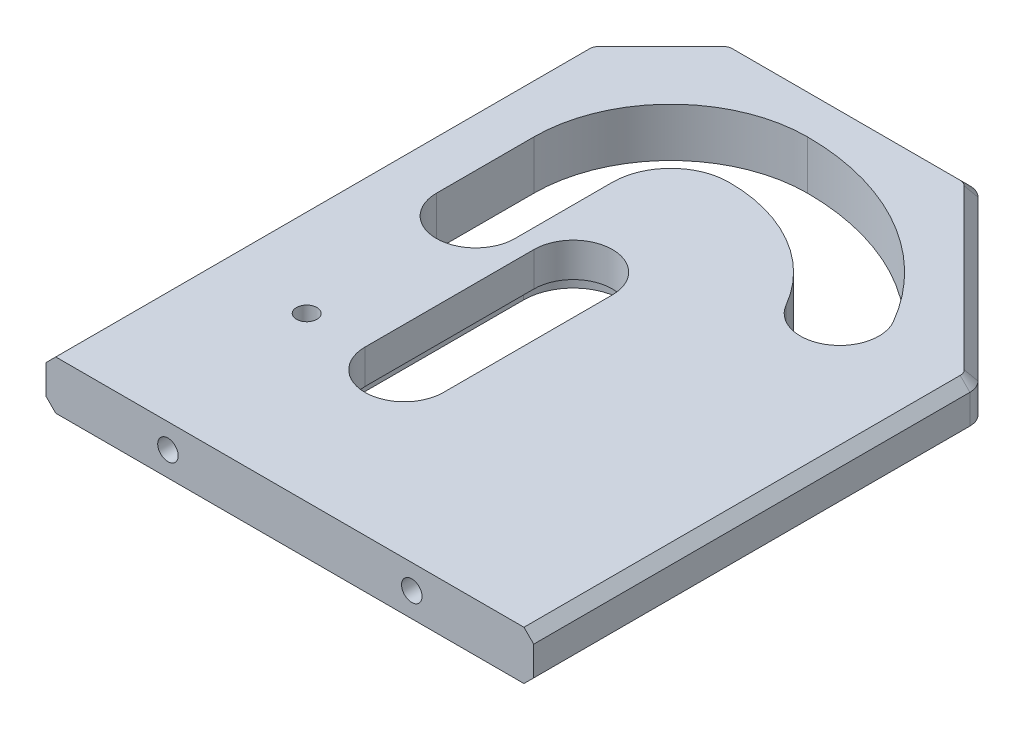
SolidWorks part; units mm, degrees
ref_plane "Front Plane" through (0, 0, 0) normal (0, 0, 1) x (1, 0, 0)
ref_plane "Top Plane" through (0, 0, 0) normal (0, 1, 0) x (1, 0, 0)
ref_plane "Right Plane" through (0, 0, 0) normal (1, 0, 0) x (0, 0, -1)
sketch "Sketch1" plane through (0, 0, 0) normal (0, 1, 0) x (1, 0, 0)
  line L1 (-40, -68.0944) -> (60, -68.0944)
  line L2 (-40, -68.0944) -> (-40, 58)
  line L3 (-40, 58) -> (60, 58)
  line L4 (60, -68.0944) -> (60, 58)
  dimension "D1" = 68.0944
  dimension "D2" = 40
  dimension "D3" = 58
  dimension "D4" = 60
extrude "Boss-Extrude1" add sketch "Sketch1" along normal mid plane 10
sketch "Slots Path" plane through (0, 0, 0) normal (0, 1, 0) x (1, 0, 0)
  line L2 (-20, 0) -> (-20, 20)
  line L3 (0, 0) -> (0, -34.641)
  line L4 (-5.5, 0) -> (5.5, 0) construction
  arc A1 (0, 40) -> (-20, 20) centre (0, 20) ccw
  arc A2 (0, 40) -> (34.641, 20) centre (0, 0) cw
  point P1 (-20, -34.641)
  dimension "D1" = 20
  dimension "D2" = 40
  dimension "D3" = 20
  dimension "D4" = 20
  dimension "D5" = 40
sketch "Sketch3" plane through (0, 5, 0) normal (0, 1, 0) x (1, 0, 0)
  line L9 (-8.05, 0) -> (-8.05, -34.641)
  line L10 (-11.95, 0) -> (-11.95, 20)
  line L11 (-28.05, 0) -> (-28.05, 20)
  line L12 (8.05, 0) -> (8.05, -34.641)
  arc A2 (-8.05, 0) -> (8.05, 0) centre (0, 0) cw
  arc A3 (-8.05, -34.641) -> (8.05, -34.641) centre (0, -34.641) ccw
  arc A18 (0, 31.95) -> (-11.95, 20) centre (0, 20) ccw
  arc A19 (27.6695, 15.975) -> (0, 31.95) centre (0, 0) ccw
  arc A20 (0, 48.05) -> (-28.05, 20) centre (0, 20) ccw
  arc A21 (41.6125, 24.025) -> (0, 48.05) centre (0, 0) ccw
  arc A22 (-11.95, 0) -> (-28.05, 0) centre (-20, 0) cw
  arc A23 (27.6695, 15.975) -> (41.6125, 24.025) centre (34.641, 20) ccw
extrude "Slots" cut sketch "Sketch3" against normal through all
sketch "Sketch12" plane through (0, -5, 0) normal (0, -1, 0) x (1, 0, 0)
  line L2 (10.15, 0) -> (10.15, 34.641)
  line L3 (-10.15, 0) -> (-10.15, 34.641)
  arc A0 (10.15, 0) -> (-10.15, 0) centre (0, 0) cw
  arc A1 (10.15, 34.641) -> (-10.15, 34.641) centre (0, 34.641) ccw
extrude "Cut-Extrude6" cut sketch "Sketch12" against normal blind 3
hole_wizard "M5x0.8 Tapped Hole2" positions "Sketch8" profile "Sketch9" tap size "M5x0.8" standard "ANSI Metric" end condition through all
sketch "Sketch8" plane through (0, 5, 0) normal (0, 1, 0) x (1, 0, 0)
  point P0 (-20, -34.641)
cosmetic thread "Hole Thread3" parameters "D2"=5
sketch "Sketch9" plane through (-20, 5, 34.641) normal (1, 0, 0) x (0, 0, 1)
  line L0 (0, 0) -> (0, 10)
  line L1 (0, 10) -> (2.1, 10)
  line L2 (2.1, 10) -> (2.1, 0)
  line L5 (2.1, 0) -> (0, 0)
  line L11 (0, -6.35) -> (0, 107.95) construction
  dimension "Thru Tap Drill Dia." = 4.2
  dimension "Thru Tap Drill Depth" = 10
sketch "Sketch13" plane through (0, -5, 0) normal (0, -1, 0) x (1, 0, 0)
  circle A0 centre (-20, 34.641) radius 4.15
  dimension "D1" = 8.3
extrude "Cut-Extrude7" cut sketch "Sketch13" against normal blind 5
hole_wizard "M5x0.8 Tapped Hole1" positions "Sketch6" profile "Sketch7" tap size "M5x0.8" standard "ANSI Metric"
sketch "Sketch6" plane through (0, 0, 68.0944) normal (0, 0, 1) x (1, 0, 0)
  line L0 (55, 0) -> (-55, 0) construction
  line L1 (-40, 5) -> (-40, -5) construction
  line L2 (60, 5) -> (60, -5) construction
  point P0 (-15, 0)
  point P2 (35, 0)
  point P11 (-40, 0)
  dimension "D1" = 25
  dimension "D2" = 25
sketch "Sketch7" plane through (-15, 0, 68.0944) normal (1, 0, 0) x (0, -1, 0)
  line L0 (0, 0) -> (0, 21.2618)
  line L1 (0, 21.2618) -> (2.1, 20)
  line L2 (2.1, 20) -> (2.1, 0)
  line L5 (2.1, 0) -> (0, 0)
  line L10 (0, 21.2618) -> (-2.1, 20) construction
  line L11 (0, -6.35) -> (0, 107.95) construction
  dimension "Tap Drill Dia." = 4.2
  dimension "Tap Drill Depth" = 20
  dimension "Drill Angle" = 118
cosmetic thread "Hole Thread1" parameters "D1"=20, "D2"=5
cosmetic thread "Hole Thread2" parameters "D1"=20, "D2"=5
sketch "Sketch4" plane through (0, 5, 0) normal (0, 1, 0) x (1, 0, 0)
  line L0 (-40, 43) -> (-40, 58)
  line L1 (-40, 58) -> (-40, -68.0944) construction
  line L2 (-40, 58) -> (-25, 58)
  line L3 (60, 58) -> (-40, 58) construction
  line L4 (-25, 58) -> (-40, 43)
  dimension "D1" = 15
  dimension "D2" = 15
extrude "Cut-Extrude2" cut sketch "Sketch4" against normal through all
sketch "Sketch5" plane through (0, 5, 0) normal (0, 1, 0) x (1, 0, 0)
  line L0 (25, 58) -> (60, 58)
  line L1 (60, 58) -> (-25, 58) construction
  line L2 (60, 58) -> (60, 23)
  line L3 (60, -68.0944) -> (60, 58) construction
  line L4 (60, 23) -> (25, 58)
  dimension "D1" = 35
  dimension "D2" = 35
extrude "Cut-Extrude3" cut sketch "Sketch5" against normal through all
fillet "Fillet1" radius 4 4 edges at (60, 0, -23) (25, 0, -58) (-25, 0, -58) (-40, 0, -43)
chamfer "Chamfer1" distance 2 angle 45 18 edges at (60, -5, 23.3756) (42.5, -5, -40.5) (0, -5, -58) (-32.5, -5, -50.5) (-40, -5, 13.3756) (60, 5, 23.3756) (42.5, 5, -40.5) (0, 5, -58) (-32.5, 5, -50.5) (-40, 5, 13.3756) (59.6955, -5, -22.8739) (24.8739, -5, -57.6955) (-24.8739, -5, -57.6955) (-39.6955, -5, -42.8739) (59.6955, 5, -22.8739) (24.8739, 5, -57.6955) (-24.8739, 5, -57.6955) (-39.6955, 5, -42.8739)
